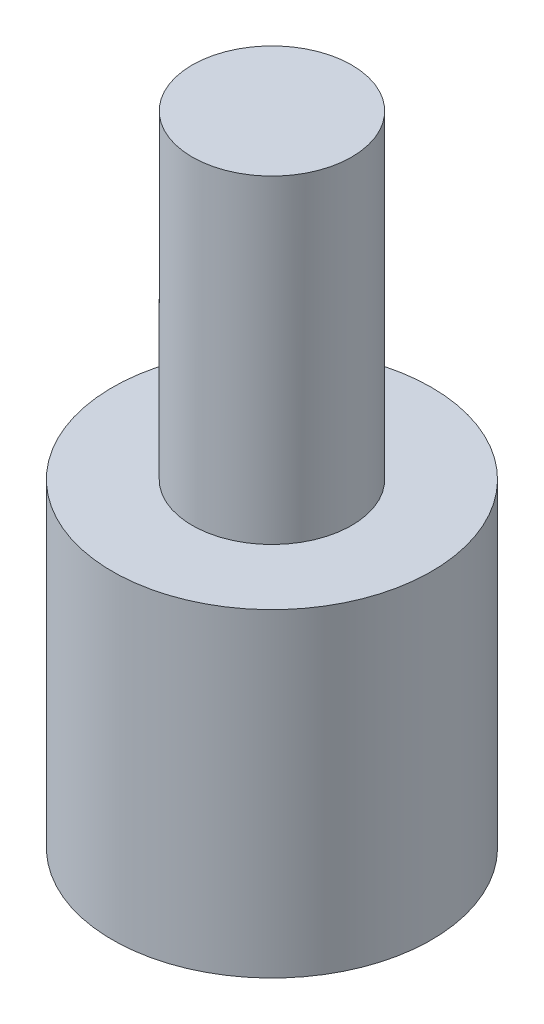
SolidWorks part; units mm, degrees
ref_plane "Ebene vorne" through (0, 0, 0) normal (0, 0, 1) x (1, 0, 0)
ref_plane "Ebene oben" through (0, 0, 0) normal (0, 1, 0) x (1, 0, 0)
ref_plane "Ebene rechts" through (0, 0, 0) normal (1, 0, 0) x (0, 0, -1)
sketch "Skizze1" plane through (0, 0, 0) normal (0, 1, 0) x (1, 0, 0)
  circle A0 centre (0, 0) radius 2.5
  dimension "D1" = 5
extrude "Aufsatz-Linear austragen1" add sketch "Skizze1" along normal blind 10
sketch "Skizze2" plane through (0, 0, 0) normal (0, -1, 0) x (1, 0, 0)
  circle A0 centre (0, 0) radius 5
  dimension "D1" = 10
extrude "Aufsatz-Linear austragen2" add sketch "Skizze2" along normal blind 10
ref_plane "Ebene1" through (0, 5, 0) normal (0, 1, 0) x (1, 0, 0)
